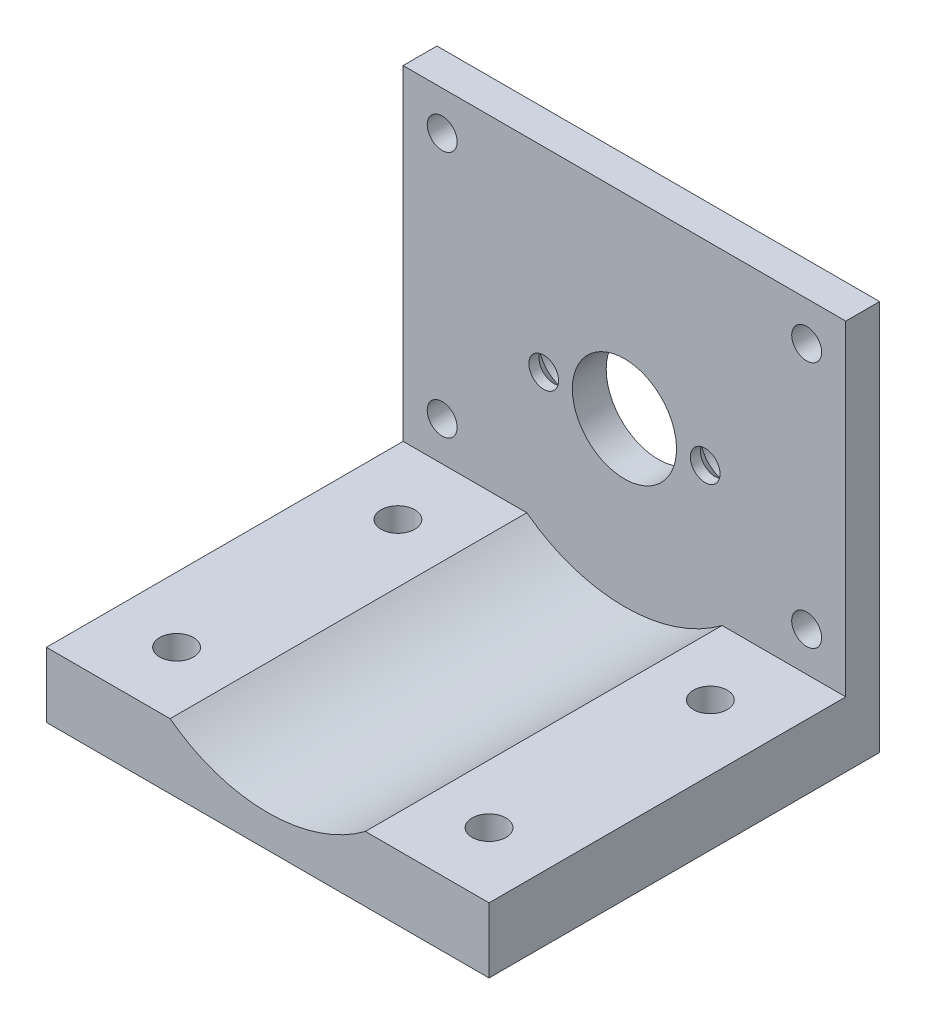
SolidWorks part; units mm, degrees
material "ABS"
ref_plane "Front Plane" through (0, 0, 0) normal (0, 0, 1) x (1, 0, 0)
ref_plane "Top Plane" through (0, 0, 0) normal (0, 1, 0) x (1, 0, 0)
ref_plane "Right Plane" through (0, 0, 0) normal (1, 0, 0) x (0, 0, -1)
sketch "Sketch2" plane through (0, 0, 0) normal (0, 0, 1) x (1, 0, 0)
  line L1 (0, 0) -> (43.18, 0)
  line L2 (0, 0) -> (0, 38.1)
  line L3 (0, 38.1) -> (43.18, 38.1)
  line L4 (43.18, 0) -> (43.18, 38.1)
  dimension "D1" = 38.1
  dimension "D2" = 43.18
extrude "Boss-Extrude1" add sketch "Sketch2" along normal blind 3.302
sketch "Sketch4" plane through (0, 0, 0) normal (0, 0, -1) x (-1, 0, 0)
  line L0 (-43.18, 19.05) -> (0, 19.05) construction
  line L1 (-43.18, 0) -> (-43.18, 38.1) construction
  line L2 (0, 38.1) -> (0, 0) construction
  line L3 (-21.59, 38.1) -> (-21.59, 0) construction
  line L4 (-43.18, 38.1) -> (0, 38.1) construction
  line L5 (0, 0) -> (-43.18, 0) construction
  line L6 (-43.18, 38.1) -> (0, 38.1) construction
  circle A0 centre (-21.59, 19.05) radius 5.08
  circle A1 centre (-3.81, 34.29) radius 1.4605
  circle A2 centre (-3.81, 10.16) radius 1.4605
  circle A3 centre (-39.37, 10.16) radius 1.4605
  circle A4 centre (-39.37, 34.29) radius 1.4605
  dimension "D1" = 10.16
  dimension "D2" = 19.05
  dimension "D3" = 17.78
  dimension "D4" = 3.81
  dimension "D5" = 2.921
  dimension "D7" = 21.59
  dimension "D6" = 27.94
extrude "Cut-Extrude1" cut sketch "Sketch4" against normal through all
hole_wizard "CSK for M2.5 Oval Head Machine Screw1" positions "3DSketch1" profile "Sketch7" countersink size "M2.5" standard "ANSI Metric" end condition through all
sketch3d "3DSketch1"
  line L0 (43.18, 38.1, 0) -> (0, 38.1, 0) construction
  line L1 (21.59, 38.1, 0) -> (21.59, 0, 0) construction
  line L2 (0, 0, 0) -> (43.18, 0, 0) construction
  point P0 (29.464, 19.05, 0)
  point P2 (13.716, 19.05, 0)
  point P14 (21.59, 19.05, 0)
  dimension "D1" = 19.05
  dimension "D4" = 19.05
  dimension "D2" = 7.874
  dimension "D3" = 7.874
sketch "Sketch7" plane through (29.464, 19.05, 0) normal (1, 0, 0) x (0, 1, 0)
  line L0 (0, 0) -> (0, 3.302)
  line L1 (0, 3.302) -> (1.45, 3.302)
  line L2 (1.45, 3.302) -> (1.45, 2.316)
  line L3 (1.45, 2.316) -> (2.75, 1.016)
  line L4 (2.75, 1.016) -> (2.75, 0)
  line L6 (2.75, 0) -> (0, 0)
  line L7 (-1.45, 2.316) -> (-2.75, 1.016) construction
  line L11 (0, -6.35) -> (0, 107.95) construction
  dimension "Thru Hole Dia." = 2.9
  dimension "Thru Hole Depth" = 3.302
  dimension "C'Sink Dia." = 5.5
  dimension "C'Sink Angle" = 90
  dimension "Head Clearance" = 1.016
sketch "Sketch8" plane through (0, 0, 3.302) normal (0, 0, 1) x (1, 0, 0)
  line L0 (0, 6.35) -> (43.18, 6.35) construction
  line L1 (0, 38.1) -> (0, 0) construction
  line L2 (43.18, 0) -> (43.18, 38.1) construction
  line L3 (0, 0) -> (43.18, 0) construction
  line L4 (21.59, 38.1) -> (21.59, 0) construction
  line L5 (43.18, 38.1) -> (0, 38.1) construction
  line L6 (0, 19.05) -> (43.18, 19.05) construction
  line L7 (31.115, 6.35) -> (43.18, 6.35)
  line L8 (12.065, 6.35) -> (0, 6.35)
  line L9 (0, 6.35) -> (0, 0)
  line L10 (0, 0) -> (43.18, 0)
  line L11 (43.18, 0) -> (43.18, 6.35)
  arc A0 (12.065, 6.35) -> (31.115, 6.35) centre (21.59, 19.05) ccw
  point P14 (21.59, 19.05)
  point P15 (21.59, 19.05)
  dimension "D2" = 15.875
  dimension "D1" = 6.35
extrude "Boss-Extrude2" add sketch "Sketch8" along normal blind 38.1 from surface at -3.302 starting at face at (26.714, 19.05, 0)
sketch "Sketch9" plane through (0, 6.35, 0) normal (0, 1, 0) x (1, 0, 0)
  line L0 (0, -38.1) -> (0, -3.302) construction
  line L1 (12.065, -38.1) -> (0, -38.1) construction
  line L2 (21.59, -38.1) -> (21.59, -3.302) construction
  line L3 (12.065, -38.1) -> (31.115, -38.1) construction
  line L4 (12.065, -3.302) -> (31.115, -3.302) construction
  circle A0 centre (6.35, -31.75) radius 1.651
  circle A1 centre (6.35, -10.16) radius 1.651
  circle A2 centre (36.83, -10.16) radius 1.651
  circle A3 centre (36.83, -31.75) radius 1.651
  dimension "D1" = 3.302
  dimension "D2" = 6.35
  dimension "D3" = 6.35
  dimension "D4" = 21.59
  dimension "D5" = 30.48
extrude "Cut-Extrude2" cut sketch "Sketch9" against normal through all
sketch "Sketch10" plane through (0, 0, 0) normal (0, 0, -1) x (-1, 0, 0)
  line L0 (-21.59, 30.2895) -> (-21.59, 32.8295) construction
  line L1 (-21.59, 24.13) -> (-21.59, 26.67) construction
  line L2 (-37.0642, 26.67) -> (-6.1158, 26.67) construction
  line L3 (-37.0642, 26.67) -> (-43.18, 26.67) construction
  line L4 (-43.18, 0) -> (-43.18, 38.1) construction
  line L5 (-6.1158, 26.67) -> (0, 26.67) construction
  line L6 (0, 38.1) -> (0, 0) construction
  line L7 (-37.0642, 26.67) -> (-37.0642, 30.2895) construction
  line L8 (-37.0642, 30.2895) -> (-6.1158, 30.2895) construction
  line L9 (-6.1158, 30.2895) -> (-6.1158, 26.67) construction
  line L10 (-39.37, 32.8295) -> (-3.81, 32.8295) construction
  circle A1 centre (-21.59, 19.05) radius 5.08 construction
  circle A2 centre (-39.37, 34.29) radius 1.4605 construction
  circle A3 centre (-3.81, 34.29) radius 1.4605 construction
  text T0 "Jack Goodwin" font "Century Gothic" height in points 12
  dimension "D1" = 2.54
  dimension "D2" = 6.1158
extrude "Cut-Extrude3" cut sketch "Sketch10" against normal blind 1.27
